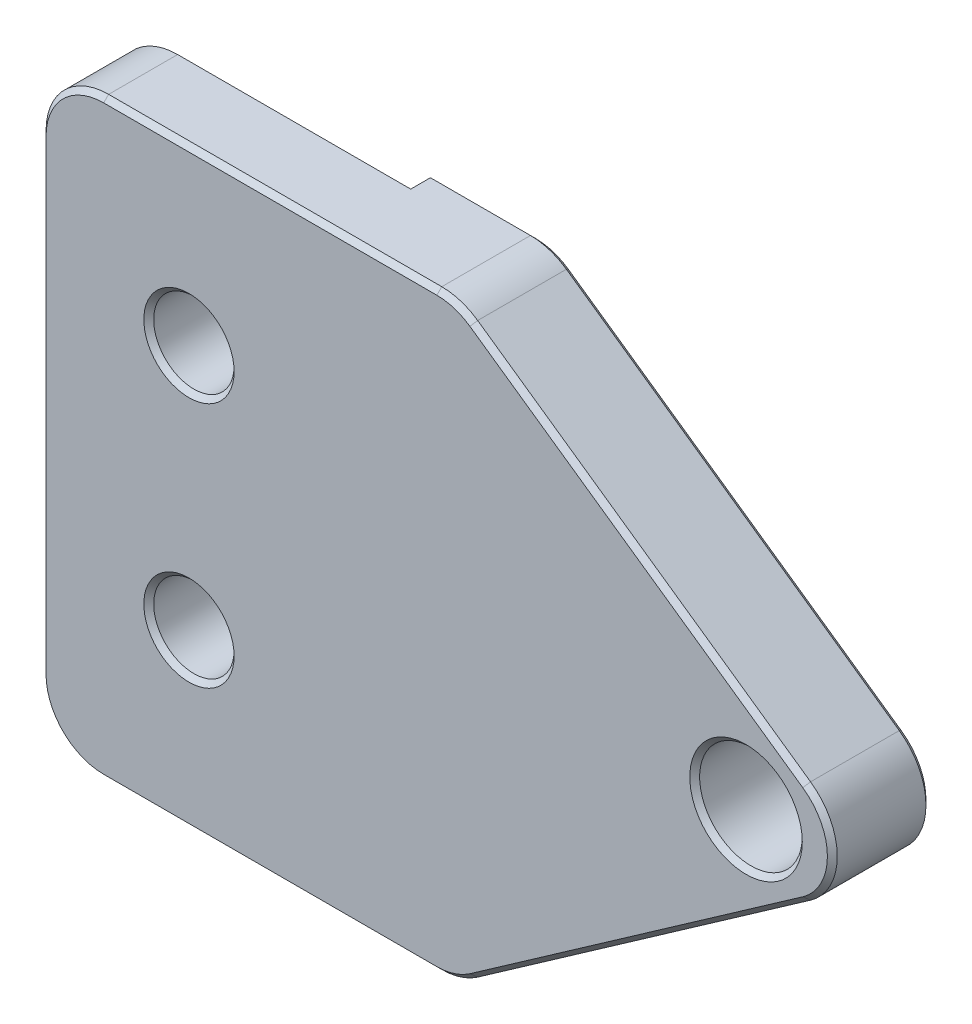
SolidWorks part; units mm, degrees
material "6061-T6 Al"
ref_plane "Front" through (0, 0, 0) normal (0, 0, 1) x (1, 0, 0)
ref_plane "Top" through (0, 0, 0) normal (0, 1, 0) x (1, 0, 0)
ref_plane "Right" through (0, 0, 0) normal (1, 0, 0) x (0, 0, -1)
sketch "Sketch1" plane through (0, 0, 0) normal (0, 0, 1) x (1, 0, 0)
  line L0 (0, 0) -> (-17.1378, 12)
  line L1 (-17.1378, 12) -> (-34, 12)
  line L2 (-34, 12) -> (-34, 0)
  line L3 (-34, 0) -> (-34, -12)
  line L4 (-34, -12) -> (-17.1378, -12)
  line L5 (-17.1378, -12) -> (0, 0)
  dimension "D1" = 70
  dimension "D2" = 34
  dimension "D3" = 12
extrude "Extrude1" add sketch "Sketch1" along normal blind 4
sketch "Sketch2" plane through (0, 12, 0) normal (0, 1, 0) x (1, 0, 0)
  line L1 (-34, 0) -> (-22, 0)
  line L2 (-34, 0) -> (-34, -1)
  line L3 (-34, -1) -> (-22, -1)
  line L4 (-22, 0) -> (-22, -1)
  dimension "D1" = 12
  dimension "D2" = 1
extrude "Extrude2" cut sketch "Sketch2" against normal through all
ref_plane "Plane1" through (0, 0, 0) normal (0, 1, 0) x (-1, 0, 0)
hole_wizard "#4 Clearance Hole1" positions "3DSketch1" profile "Sketch3" hole size "#4" standard "Ansi Inch"
sketch3d "3DSketch1"
  line L0 (0, 0, 4) -> (-34, 0, 4) construction
  line L1 (-34, 12, 4) -> (-34, -12, 4) construction
  point P0 (-28, 5, 4)
  point P2 (-28, -5, 4)
  dimension "D1" = 6
  dimension "D2" = 5
  dimension "D3" = 5
sketch "Sketch3" plane through (-28, 5, 4) normal (1, 0, 0) x (0, -1, 0)
  line L0 (0, 0) -> (0, 9.3626)
  line L1 (0, 9.3626) -> (1.6319, 8.382)
  line L2 (1.6319, 8.382) -> (1.6319, 0)
  line L5 (1.6319, 0) -> (0, 0)
  line L10 (0, 9.3626) -> (-1.632, 8.382) construction
  line L11 (0, -6.35) -> (0, 107.95) construction
  dimension "Hole Dia." = 3.2639
  dimension "Hole Depth" = 8.382
  dimension "Drill Angle" = 118
hole_wizard "#8-32 Tapped Hole1" positions "3DSketch2" profile "Sketch4" tap size "#8-32" standard "Ansi Inch"
sketch3d "3DSketch2"
  line L0 (-34, 12, 4) -> (-34, -12, 4) construction
  point P0 (-5.39, 0, 4)
  dimension "D1" = 28.61
sketch "Sketch4" plane through (-5.39, 0, 4) normal (1, 0, 0) x (0, -1, 0)
  line L0 (0, 0) -> (0, 11.7566)
  line L1 (0, 11.7566) -> (1.7272, 10.7188)
  line L2 (1.7272, 10.7188) -> (1.7272, 8.3312)
  line L3 (1.7272, 8.3312) -> (2.0828, 8.3312)
  line L4 (2.0828, 8.3312) -> (2.0828, 0)
  line L5 (2.0828, 0) -> (0, 0)
  line L10 (0, 11.7566) -> (-1.7272, 10.7188) construction
  line L11 (0, -6.35) -> (0, 107.95) construction
  dimension "Tap Drill Dia." = 3.4544
  dimension "Tap Drill Depth" = 10.7188
  dimension "Thread Major Dia." = 4.1656
  dimension "Thread Depth" = 8.3312
  dimension "Drill Angle" = 118
fillet "Fillet1" radius 2.54 5 edges at (-34, -12, 2.5) (-17.1378, -12, 2) (0, 0, 2) (-17.1378, 12, 2) (-34, 12, 2.5)
chamfer "Chamfer1" distance 0.2 angle 45 20 edges at (-33.2561, 11.2561, 4) (-24.6993, 12, 4) (-17.1748, 11.8824, 4) (-9.7266, 6.8106, 4) (-1.8884, 0, 4) (-9.7266, -6.8106, 4) (-17.1748, -11.8824, 4) (-24.6993, -12, 4) (-33.2561, -11.2561, 4) (-34, 0, 4) (-26.3681, -5, 4) (-26.3681, 5, 4) (-3.3072, 0, 4) (-19.9693, -12, 0) (-17.1748, -11.8824, 0) (-9.7266, -6.8106, 0) (-1.8884, 0, 0) (-9.7266, 6.8106, 0) (-17.1748, 11.8824, 0) (-19.9693, 12, 0)
